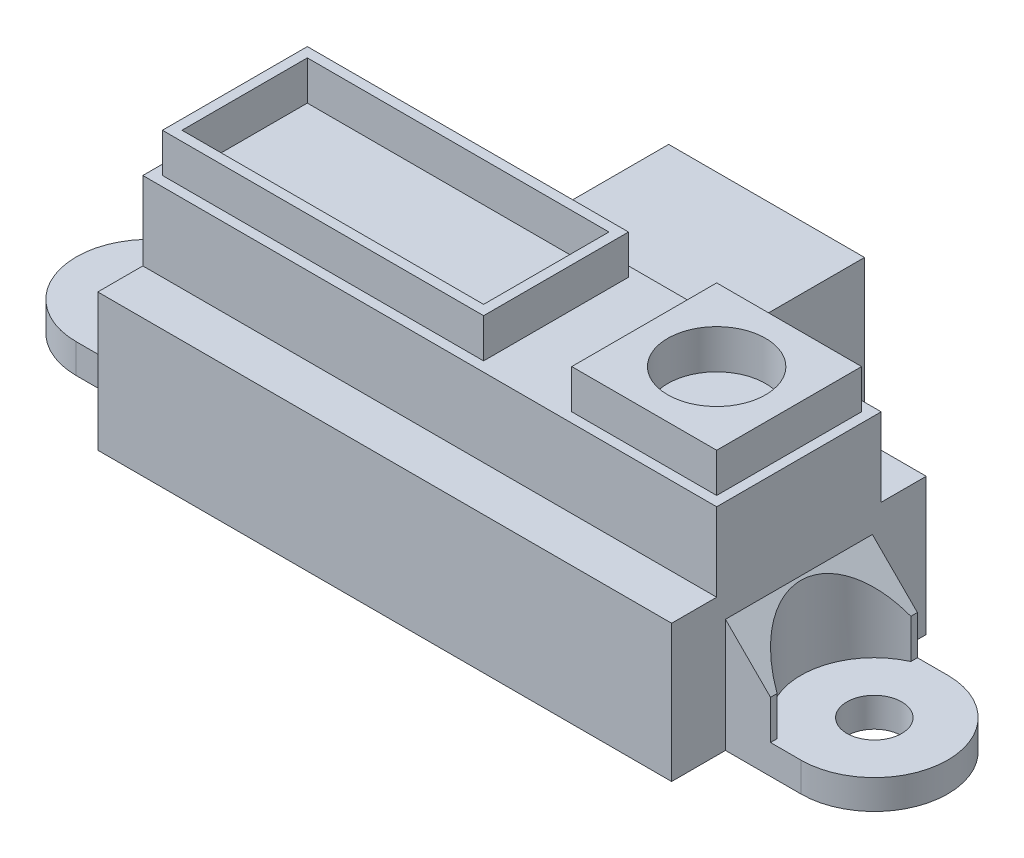
SolidWorks part; units mm, degrees
ref_plane "前视基准面" through (0, 0, 0) normal (0, 0, 1) x (1, 0, 0)
ref_plane "上视基准面" through (0, 0, 0) normal (0, 1, 0) x (1, 0, 0)
ref_plane "右视基准面" through (0, 0, 0) normal (1, 0, 0) x (0, 0, -1)
sketch "草图1" plane through (0, 0, 0) normal (0, 1, 0) x (1, 0, 0)
  line L1 (-14.65, 6.5) -> (14.65, 6.5)
  line L2 (-14.65, 6.5) -> (-14.65, -6.5)
  line L3 (-14.65, -6.5) -> (14.65, -6.5)
  line L4 (14.65, 6.5) -> (14.65, -6.5)
  line L5 (-14.65, 6.5) -> (14.65, -6.5) construction
  line L6 (-14.65, -6.5) -> (14.65, 6.5) construction
  point P0 (0, 0)
  dimension "D1" = 13
  dimension "D2" = 29.3
extrude "凸台-拉伸1" add sketch "草图1" along normal blind 7
sketch "草图2" plane through (0, 7, 0) normal (0, 1, 0) x (1, 0, 0)
  line L0 (14.65, -6.5) -> (14.65, 6.5) construction
  line L1 (-14.65, -4.2) -> (14.65, -4.2)
  line L2 (-14.65, -4.2) -> (-14.65, 4.2)
  line L3 (-14.65, 4.2) -> (14.65, 4.2)
  line L4 (14.65, -4.2) -> (14.65, 4.2)
  line L5 (-14.65, -4.2) -> (14.65, 4.2) construction
  line L6 (-14.65, 4.2) -> (14.65, -4.2) construction
  point P0 (0, 0)
  dimension "D1" = 8.4
extrude "凸台-拉伸2" add sketch "草图2" along normal blind 4
sketch "草图3" plane through (0, 11, 0) normal (0, 1, 0) x (1, 0, 0)
  line L0 (-14.65, 4.2) -> (-14.65, -4.2) construction
  line L1 (2.25, -3.7) -> (-14.15, -3.7)
  line L2 (2.25, -3.7) -> (2.25, 3.7)
  line L3 (2.25, 3.7) -> (-14.15, 3.7)
  line L4 (-14.15, -3.7) -> (-14.15, 3.7)
  line L5 (2.25, -3.7) -> (-14.15, 3.7) construction
  line L6 (2.25, 3.7) -> (-14.15, -3.7) construction
  line L7 (1.75, 3.2) -> (-13.65, 3.2)
  line L8 (-13.65, -3.2) -> (-13.65, 3.2)
  line L9 (1.75, -3.2) -> (-13.65, -3.2)
  line L10 (1.75, -3.2) -> (1.75, 3.2)
  line L12 (14.65, -4.2) -> (14.65, 4.2) construction
  line L13 (6.75, 3.7) -> (14.15, 3.7)
  line L14 (6.75, 3.7) -> (6.75, -3.7)
  line L15 (6.75, -3.7) -> (14.15, -3.7)
  line L16 (14.15, 3.7) -> (14.15, -3.7)
  line L17 (6.75, 3.7) -> (14.15, -3.7) construction
  line L18 (6.75, -3.7) -> (14.15, 3.7) construction
  circle A0 centre (10.45, 0) radius 2.5
  point P0 (-5.95, 0)
  point P12 (10.45, 0)
  dimension "D6" = 5
  dimension "D1" = 16.4
  dimension "D2" = 7.4
  dimension "D3" = 0.5
  dimension "D5" = 0.5
  dimension "D4" = 0.5
extrude "凸台-拉伸3" add sketch "草图3" along normal blind 2
sketch "草图5" plane through (0, 0, 0) normal (0, 1, 0) x (1, 0, 0)
  line L0 (0, 0) -> (0, -20.4049) construction
  line L1 (-18.5, 3.75) -> (18.5, 3.75)
  line L3 (-18.5, -3.75) -> (18.5, -3.75)
  line L5 (-18.5, 3.75) -> (18.5, -3.75) construction
  line L6 (-18.5, -3.75) -> (18.5, 3.75) construction
  arc A0 (18.5, -3.75) -> (18.5, 3.75) centre (18.5, 0) ccw
  arc A1 (-18.5, 3.75) -> (-18.5, -3.75) centre (-18.5, 0) ccw
  circle A2 centre (18.5, 0) radius 1.4
  circle A3 centre (-18.5, 0) radius 1.4
  point P0 (0, 0)
  dimension "D2" = 2.8
  dimension "D1" = 7.5
  dimension "D3" = 37
extrude "凸台-拉伸4" add sketch "草图5" along normal blind 5.8
sketch "草图6" plane through (0, 0, 0) normal (0, 0, 1) x (1, 0, 0)
  line L0 (0, 0) -> (0, 27.0871) construction
  line L1 (-22.25, 1.5) -> (-16.95, 1.5)
  line L2 (-22.25, 5.8) -> (-22.25, 0) construction
  line L3 (-16.95, 1.5) -> (-16.95, 3.5)
  line L4 (-16.95, 3.5) -> (-14.65, 5.8)
  line L5 (-14.65, 5.8) -> (-22.25, 5.8)
  line L6 (-22.25, 5.8) -> (-22.25, 1.5)
  line L7 (-22.25, 0) -> (-18.5, 0) construction
  line L8 (-14.65, 7) -> (-14.65, 0) construction
  line L9 (22.25, 5.8) -> (22.25, 1.5)
  line L10 (14.65, 5.8) -> (22.25, 5.8)
  line L11 (16.95, 3.5) -> (14.65, 5.8)
  line L12 (16.95, 1.5) -> (16.95, 3.5)
  line L13 (22.25, 1.5) -> (16.95, 1.5)
  dimension "D1" = 1.5
  dimension "D2" = 2.3
  dimension "D3" = 2
extrude "切除-拉伸1" cut sketch "草图6" against normal mid plane 10
sketch "草图7" plane through (0, 1.5, 0) normal (0, 1, 0) x (1, 0, 0)
  circle A0 centre (18.5, 0) radius 3.75
  circle A1 centre (-18.5, 0) radius 3.75
extrude "切除-拉伸2" cut sketch "草图7" along normal blind 10
sketch "草图8" plane through (0, 0, -6.5) normal (0, 0, -1) x (-1, 0, 0)
  line L0 (-2.25, 13) -> (14.15, 13) construction
  line L1 (-5, 1.6) -> (5, 1.6)
  line L2 (-5, 1.6) -> (-5, 8.6)
  line L3 (-5, 8.6) -> (5, 8.6)
  line L4 (5, 1.6) -> (5, 8.6)
  line L5 (-5, 1.6) -> (5, 8.6) construction
  line L6 (-5, 8.6) -> (5, 1.6) construction
  point P0 (0, 5.1)
  dimension "D1" = 10
  dimension "D2" = 7
  dimension "D3" = 4.4
extrude "凸台-拉伸5" add sketch "草图8" along normal blind 6.5 and the other way up to next
